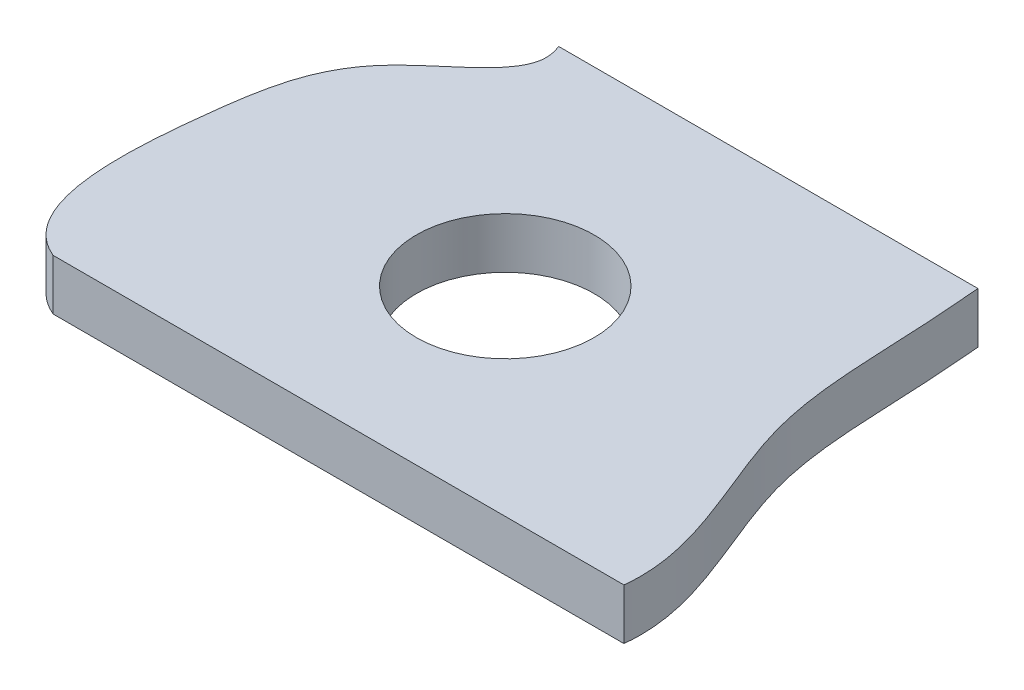
SolidWorks part; units mm, degrees
ref_plane "Front" through (0, 0, 0) normal (0, 0, 1) x (1, 0, 0)
ref_plane "Top" through (0, 0, 0) normal (0, 1, 0) x (1, 0, 0)
ref_plane "Right" through (0, 0, 0) normal (1, 0, 0) x (0, 0, -1)
sketch "Szkic1" plane through (0, 0, 0) normal (0, 1, 0) x (1, 0, 0)
  line L1 (-97.6782, 49.4149) -> (-32.7448, 49.4149)
  line L3 (-112.0276, -12.3687) -> (-49.7154, -12.3687)
  spline S0 degree 3 poles (-97.6782, 49.4149) (-95.9969, 42.8176) (-98.2137, 28.3282) (-109.2156, 9.1916) (-111.9191, -6.7183) (-112.0276, -12.3687) knots 0.127639 0.127639 0.127639 0.127639 0.284871 0.500246 0.624009 0.624009 0.624009 0.624009
  spline S1 degree 3 poles (-32.7448, 49.4149) (-29.3063, 38.4824) (-35.0861, 19.4437) (-46.8157, -0.452) (-49.5166, -11.4672) (-49.7154, -12.3687) knots 0.154589 0.154589 0.154589 0.154589 0.391686 0.611577 0.631042 0.631042 0.631042 0.631042
extrude "Dodanie-wyciągnięcie1" add sketch "Szkic1" along normal blind 3
sketch "Szkic2" plane through (0, 3, 0) normal (0, 1, 0) x (1, 0, 0)
  line L0 (-97.6782, 49.4149) -> (-49.7154, -12.3687) construction
  line L1 (-32.7448, 49.4149) -> (-112.0276, -12.3687) construction
  circle A0 centre (-73.2028, 17.8868) radius 5.25
extrude "Wytnij-wyciągnięcie1" cut sketch "Szkic2" against normal through all
sketch "Szkic3" plane through (0, 3, 0) normal (0, 1, 0) x (1, 0, 0)
  line L1 (-103.7657, 54.1446) -> (-20.7234, 54.1446)
  line L2 (-103.7657, 54.1446) -> (-103.7657, 31.7191)
  line L3 (-103.7657, 31.7191) -> (-20.7234, 31.7191)
  line L4 (-20.7234, 54.1446) -> (-20.7234, 31.7191)
  line L5 (-114.2383, 6.1212) -> (-21.8363, 6.1212)
  line L6 (-114.2383, 6.1212) -> (-114.2383, -17.1417)
  line L7 (-114.2383, -17.1417) -> (-21.8363, -17.1417)
  line L8 (-21.8363, 6.1212) -> (-21.8363, -17.1417)
extrude "Wytnij-wyciągnięcie2" cut sketch "Szkic3" against normal through all
sketch "Szkic4" plane through (0, 3, 0) normal (0, 1, 0) x (1, 0, 0)
  line L0 (-42.8443, 6.1212) -> (-108.8022, 6.1212) construction
  spline S0 degree 3 poles (-112.4736, 31.2351) (-96.1549, 43.0271) (-81.0898, 30.4652) (-89.6446, 25.5029) (-91.0943, 17.3209) (-91.8905, 4.6568) (-70.3459, 7.4082) (-112.6251, -8.4662) (-128.2548, 14.5318) (-112.4736, 31.2351) (-96.1549, 43.0271) (-81.0898, 30.4652) knots -0.479004 -0.321351 -0.212833 0 0.05631 0.10514 0.166932 0.258638 0.30517 0.520996 0.678649 0.787167 1 1.05631 1.10514 1.166932 only from (-88.6899, 36.0102) to (-88.6899, 36.0102)
  spline S1 degree 3 poles (-30.3223, 42.955) (-61.1072, 46.0703) (-58.5755, 28.2586) (-58.9254, 17.112) (-49.7054, 4.1278) (-72.0401, -9.9647) (-44.5006, -4.6313) (-29.3734, 0.7776) (-22.9732, 21.5904) (-30.3223, 42.955) (-61.1072, 46.0703) (-58.5755, 28.2586) knots -0.442045 -0.292669 -0.178763 0 0.066886 0.137582 0.239376 0.330501 0.448637 0.557955 0.707331 0.821237 1 1.066886 1.137582 1.239376 only from (-58.5068, 38.5879) to (-58.5068, 38.5879)
extrude "Wytnij-wyciągnięcie3" cut sketch "Szkic4" against normal through all
